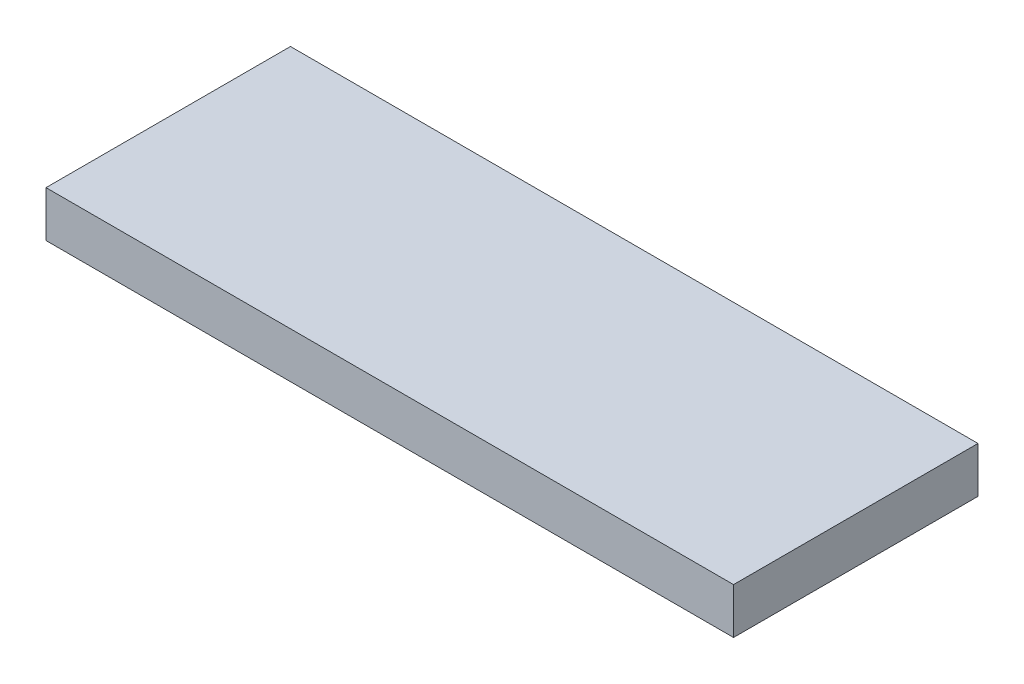
SolidWorks part; units mm, degrees
ref_plane "Front Plane" through (0, 0, 0) normal (0, 0, 1) x (1, 0, 0)
ref_plane "Top Plane" through (0, 0, 0) normal (0, 1, 0) x (1, 0, 0)
ref_plane "Right Plane" through (0, 0, 0) normal (1, 0, 0) x (0, 0, -1)
sketch "Sketch1" plane through (0, 0, 0) normal (0, 1, 0) x (1, 0, 0)
  line L1 (-92.8859, 37.6723) -> (192.8641, 37.6723)
  line L2 (-92.8859, 37.6723) -> (-92.8859, -63.9277)
  line L3 (-92.8859, -63.9277) -> (192.8641, -63.9277)
  line L4 (192.8641, 37.6723) -> (192.8641, -63.9277)
  dimension "D1" = 285.75
  dimension "D2" = 101.6
extrude "Boss-Extrude1" add sketch "Sketch1" along normal blind 19.05
